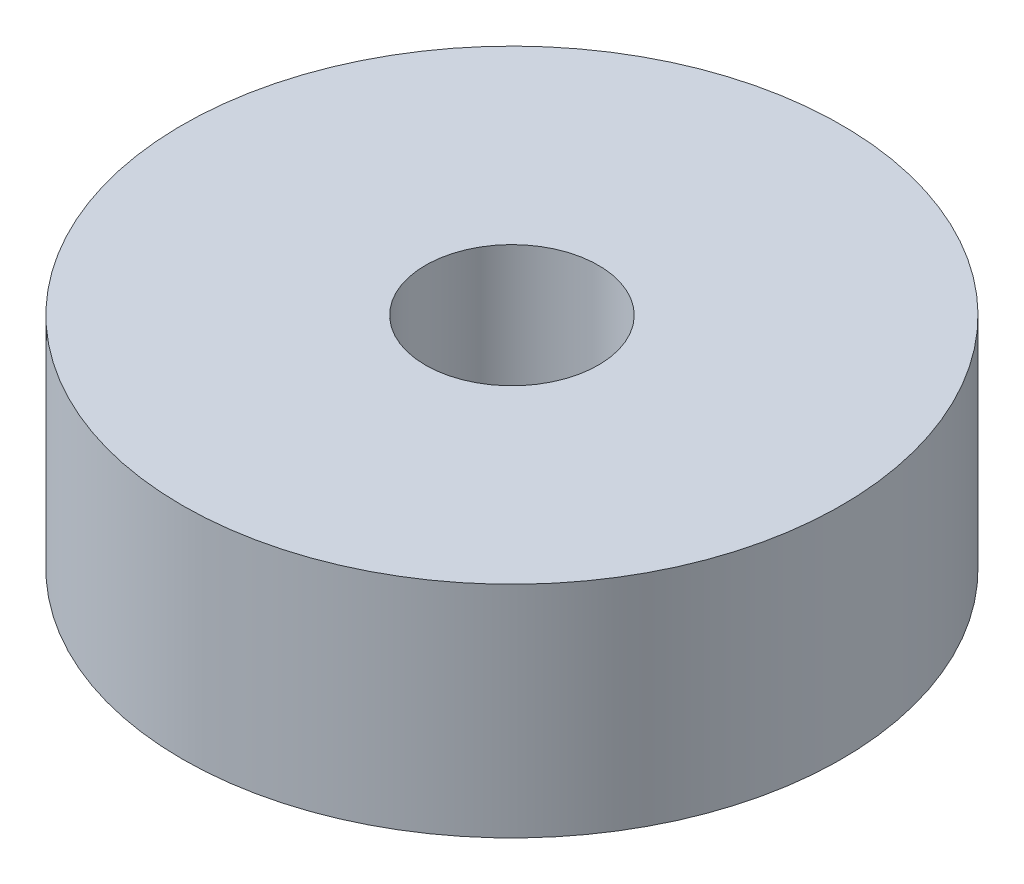
SolidWorks part; units mm, degrees
material "Polyurethane Foam Rigid"
ref_plane "Front Plane" through (0, 0, 0) normal (0, 0, 1) x (1, 0, 0)
ref_plane "Top Plane" through (0, 0, 0) normal (0, 1, 0) x (1, 0, 0)
ref_plane "Right Plane" through (0, 0, 0) normal (1, 0, 0) x (0, 0, -1)
sketch "Sketch1" plane through (0, 0, 0) normal (0, 1, 0) x (1, 0, 0)
  circle A0 centre (0, 0) radius 5
  circle A1 centre (0, 0) radius 19.05
  dimension "D1" = 10
  dimension "D2" = 38.1
extrude "Boss-Extrude1" add sketch "Sketch1" along normal blind 12.7
